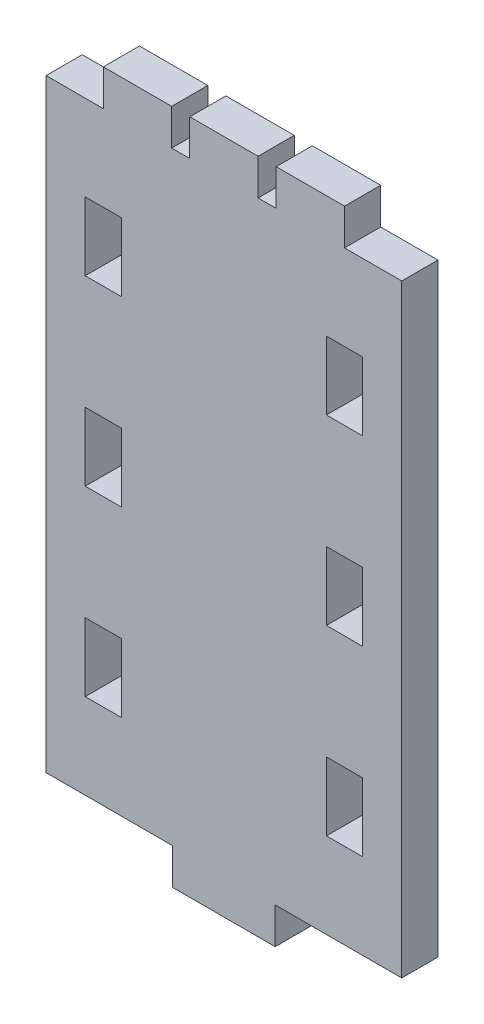
SolidWorks part; units mm, degrees
ref_plane "Front Plane" through (0, 0, 0) normal (0, 0, 1) x (1, 0, 0)
ref_plane "Top Plane" through (0, 0, 0) normal (0, 1, 0) x (1, 0, 0)
ref_plane "Right Plane" through (0, 0, 0) normal (1, 0, 0) x (0, 0, -1)
sketch "Sketch1" plane through (0, 0, 0) normal (0, 0, 1) x (1, 0, 0)
  line L0 (0, 0) -> (-11.1125, 0)
  line L1 (-11.1125, 0) -> (-11.1125, -3.175)
  line L2 (-11.1125, -3.175) -> (-20.1125, -3.175)
  line L3 (-20.1125, -3.175) -> (-20.1125, 0)
  line L4 (-20.1125, 0) -> (-31.225, 0)
  line L5 (-31.225, 0) -> (-31.225, 53)
  line L6 (-31.225, 53) -> (-26.2, 53)
  line L7 (-26.2, 53) -> (-26.2, 56.175)
  line L8 (-26.2, 56.175) -> (-20.2, 56.175)
  line L9 (-20.2, 56.175) -> (-20.2, 53)
  line L10 (-20.2, 53) -> (-18.6125, 53)
  line L11 (-18.6125, 53) -> (-18.6125, 56.175)
  line L12 (-18.6125, 56.175) -> (-12.6125, 56.175)
  line L13 (-12.6125, 56.175) -> (-12.6125, 53)
  line L14 (-12.6125, 53) -> (-11.025, 53)
  line L15 (-11.025, 53) -> (-11.025, 56.175)
  line L16 (-11.025, 56.175) -> (-5.025, 56.175)
  line L17 (-5.025, 56.175) -> (-5.025, 53)
  line L18 (-5.025, 53) -> (0, 53)
  line L19 (0, 53) -> (0, 0)
  line L20 (-15.6125, 57.9063) -> (-15.6125, -10.4437) construction
  line L21 (-15.6125, 56.175) -> (-15.6125, 48.5189) construction
  line L22 (-3.4375, 13.5) -> (-3.4375, 7.5)
  line L23 (-3.4375, 13.5) -> (-6.6125, 13.5)
  line L24 (-6.6125, 13.5) -> (-6.6125, 7.5)
  line L25 (-6.6125, 7.5) -> (-3.4375, 7.5)
  line L26 (0, 26.5) -> (-5.025, 26.5) construction
  line L27 (-5.025, 13.5) -> (-5.025, 23.5) construction
  line L28 (-5.025, 23.5) -> (-3.4375, 23.5)
  line L29 (-3.4375, 23.5) -> (-3.4375, 29.5)
  line L30 (-3.4375, 29.5) -> (-6.6125, 29.5)
  line L31 (-6.6125, 29.5) -> (-6.6125, 23.5)
  line L32 (-6.6125, 23.5) -> (-5.025, 23.5)
  line L33 (-5.025, 29.5) -> (-5.025, 39.5) construction
  line L34 (-5.025, 39.5) -> (-3.4375, 39.5)
  line L35 (-3.4375, 39.5) -> (-3.4375, 45.5)
  line L36 (-3.4375, 45.5) -> (-6.6125, 45.5)
  line L37 (-6.6125, 45.5) -> (-6.6125, 39.5)
  line L38 (-6.6125, 39.5) -> (-5.025, 39.5)
  line L39 (-26.2, 29.5) -> (-26.2, 39.5) construction
  line L40 (-26.2, 13.5) -> (-26.2, 23.5) construction
  line L41 (-24.6125, 39.5) -> (-26.2, 39.5)
  line L42 (-24.6125, 45.5) -> (-24.6125, 39.5)
  line L43 (-27.7875, 45.5) -> (-24.6125, 45.5)
  line L44 (-5.025, 45.5) -> (-5.025, 53) construction
  line L45 (-27.7875, 39.5) -> (-27.7875, 45.5)
  line L46 (-26.2, 39.5) -> (-27.7875, 39.5)
  line L47 (-24.6125, 23.5) -> (-26.2, 23.5)
  line L48 (-24.6125, 29.5) -> (-24.6125, 23.5)
  line L49 (-27.7875, 29.5) -> (-24.6125, 29.5)
  line L50 (-27.7875, 23.5) -> (-27.7875, 29.5)
  line L51 (-26.2, 23.5) -> (-27.7875, 23.5)
  line L52 (-24.6125, 7.5) -> (-27.7875, 7.5)
  line L53 (-24.6125, 13.5) -> (-24.6125, 7.5)
  line L54 (-27.7875, 13.5) -> (-24.6125, 13.5)
  line L55 (-5.025, 7.5) -> (-5.025, 0) construction
  line L56 (-27.7875, 13.5) -> (-27.7875, 7.5)
  line L61 (-5, 26.5) -> (-25.6701, 26.5) construction
  dimension "D1" = 3.175
  dimension "D2" = 3.4375
  dimension "D3" = 9
  dimension "D4" = 18
  dimension "D5" = 6
  dimension "D8" = 3.175
  dimension "D9" = 6
  dimension "D10" = 10
  dimension "D13" = 53
extrude "Boss-Extrude1" add sketch "Sketch1" along normal mid plane 3.175
